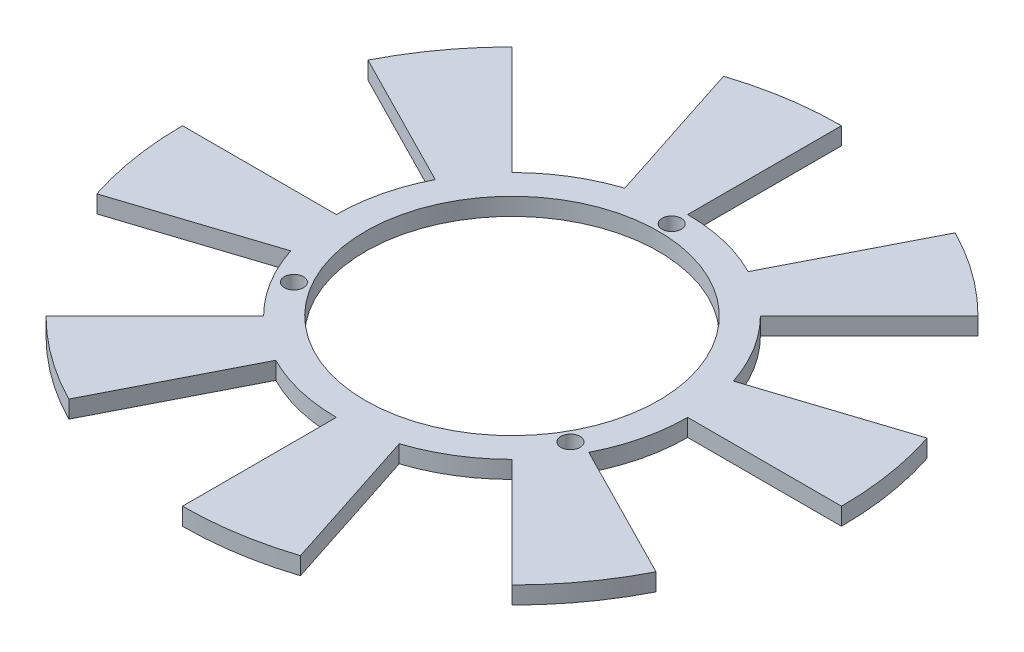
SolidWorks part; units mm, degrees
material "AISI 1010 Steel, hot rolled bar"
ref_plane "Front Plane" through (0, 0, 0) normal (0, 0, 1) x (1, 0, 0)
ref_plane "Top Plane" through (0, 0, 0) normal (0, 1, 0) x (1, 0, 0)
ref_plane "Right Plane" through (0, 0, 0) normal (1, 0, 0) x (0, 0, -1)
sketch "Sketch1" plane through (0, 0, 0) normal (0, 1, 0) x (1, 0, 0)
  circle A0 centre (0, 0) radius 25.25
  dimension "D1" = 50.5
extrude "Extrude-Thin1" add sketch "Sketch1" against normal blind 3 thin
sketch "Sketch2" plane through (0, 0, 0) normal (0, 1, 0) x (1, 0, 0)
  line L0 (0, -30.25) -> (0, 30.25) construction
  line L1 (0, 0) -> (23.8157, -13.75) construction
  line L2 (0, 0) -> (-23.8157, -13.75) construction
  circle A0 centre (0, 27.5) radius 1.65
  circle A1 centre (0, 0) radius 30.25 construction
  circle A4 centre (0, 0) radius 27.5 construction
  circle A7 centre (23.8157, -13.75) radius 1.65
  circle A8 centre (-23.8157, -13.75) radius 1.65
  dimension "D1" = 55
  dimension "D2" = 3.3
  dimension "D3" = 120
  dimension "D4" = 120
extrude "Cut-Extrude3" cut sketch "Sketch2" against normal blind 10
sketch "Sketch5" plane through (0, -3, 0) normal (0, -1, 0) x (1, 0, 0)
  line L0 (0, 0) -> (0, 35.9971) construction
  line L1 (0, 0) -> (10.5396, 32.4375) construction
  line L2 (0, 56.75) -> (0, 30.25)
  line L3 (9.3478, 28.7695) -> (17.5367, 53.9725)
  line L4 (40.1283, 40.1283) -> (21.39, 21.39)
  line L5 (26.9529, 13.7332) -> (50.5646, 25.764)
  line L6 (56.75, 0) -> (30.25, 0)
  line L7 (28.7695, -9.3478) -> (53.9725, -17.5367)
  line L8 (40.1283, -40.1283) -> (21.39, -21.39)
  line L9 (13.7332, -26.9529) -> (25.764, -50.5646)
  line L10 (0, -56.75) -> (0, -30.25)
  line L11 (-9.3478, -28.7695) -> (-17.5367, -53.9725)
  line L12 (-40.1283, -40.1283) -> (-21.39, -21.39)
  line L13 (-26.9529, -13.7332) -> (-50.5646, -25.764)
  line L14 (-56.75, 0) -> (-30.25, 0)
  line L15 (-28.7695, 9.3478) -> (-53.9725, 17.5367)
  line L16 (-40.1283, 40.1283) -> (-21.39, 21.39)
  line L17 (-13.7332, 26.9529) -> (-25.764, 50.5646)
  circle A0 centre (0, 0) radius 30.25 construction
  arc A1 (9.3478, 28.7695) -> (0, 30.25) centre (0, 0) ccw
  arc A2 (17.5367, 53.9725) -> (0, 56.75) centre (0, 0) ccw
  arc A3 (50.5646, 25.764) -> (40.1283, 40.1283) centre (0, 0) ccw
  arc A4 (26.9529, 13.7332) -> (21.39, 21.39) centre (0, 0) ccw
  arc A5 (53.9725, -17.5367) -> (56.75, 0) centre (0, 0) ccw
  arc A6 (28.7695, -9.3478) -> (30.25, 0) centre (0, 0) ccw
  arc A7 (25.764, -50.5646) -> (40.1283, -40.1283) centre (0, 0) ccw
  arc A8 (13.7332, -26.9529) -> (21.39, -21.39) centre (0, 0) ccw
  arc A9 (-17.5367, -53.9725) -> (0, -56.75) centre (0, 0) ccw
  arc A10 (-9.3478, -28.7695) -> (0, -30.25) centre (0, 0) ccw
  arc A11 (-50.5646, -25.764) -> (-40.1283, -40.1283) centre (0, 0) ccw
  arc A12 (-26.9529, -13.7332) -> (-21.39, -21.39) centre (0, 0) ccw
  arc A13 (-53.9725, 17.5367) -> (-56.75, 0) centre (0, 0) ccw
  arc A14 (-28.7695, 9.3478) -> (-30.25, 0) centre (0, 0) ccw
  arc A15 (-25.764, 50.5646) -> (-40.1283, 40.1283) centre (0, 0) ccw
  arc A16 (-13.7332, 26.9529) -> (-21.39, 21.39) centre (0, 0) ccw
  point P87 (0, 0)
  dimension "D2" = 26.5
  dimension "D1" = 18
  dimension "D3" = 8
extrude "Boss-Extrude1" add sketch "Sketch5" against normal blind 3
